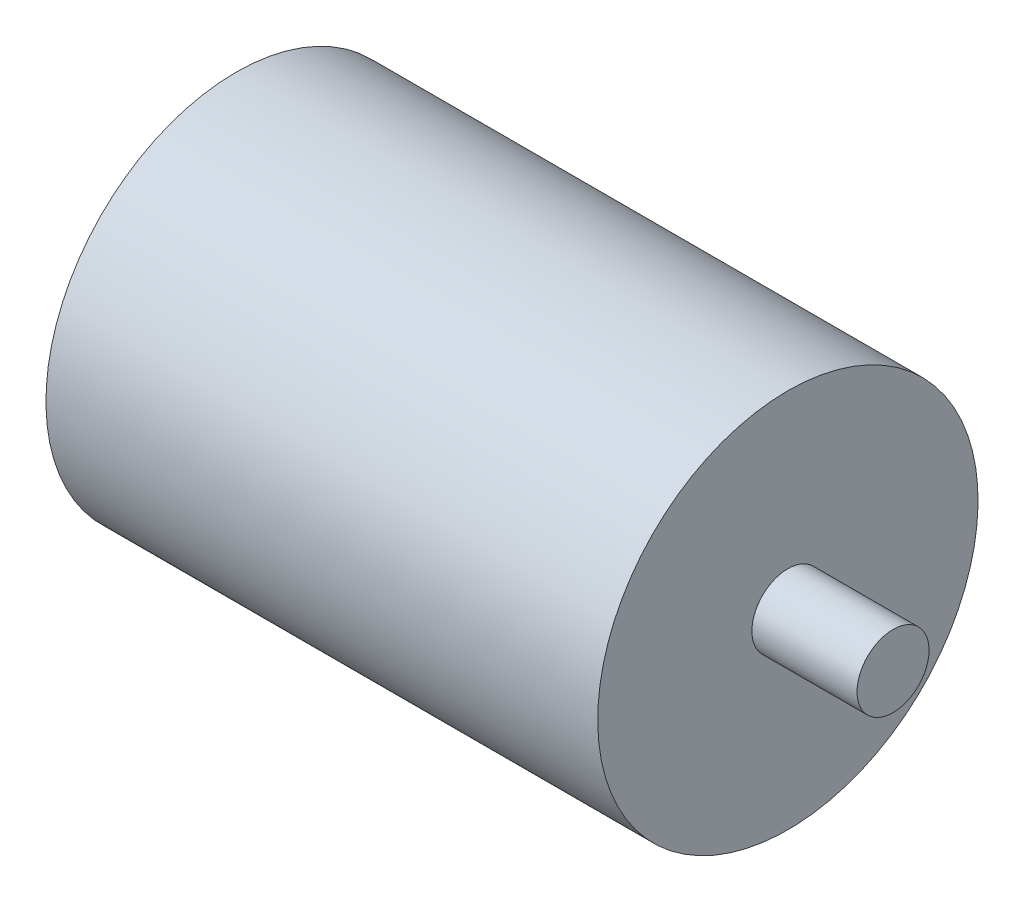
SolidWorks part; units mm, degrees
ref_plane "Front Plane" through (0, 0, 0) normal (0, 0, 1) x (1, 0, 0)
ref_plane "Top Plane" through (0, 0, 0) normal (0, 1, 0) x (1, 0, 0)
ref_plane "Right Plane" through (0, 0, 0) normal (1, 0, 0) x (0, 0, -1)
sketch "Sketch1" plane through (0, 0, 0) normal (0, 0, 1) x (1, 0, 0)
  line L0 (-48.641, 0) -> (48.641, 0)
  point P4 (0, 0)
  dimension "D1" = 97.282
sweep "Sweep1" add path "Sketch1" circular profile diameter 67.056 parameters "D3"=67.056
sketch "Sketch11" plane through (0, 0, 0) normal (0, 0, 1) x (1, 0, 0)
  line L0 (48.641, 0) -> (67.183, 0)
  line L1 (48.641, -33.528) -> (48.641, 33.528) construction
  dimension "D1" = 67.183
sweep "Sweep2" add path "Sketch11" circular profile diameter 12.7 parameters "D3"=12.7
sketch "Sketch30" plane through (0, 0, 0) normal (0, 0, 1) x (1, 0, 0)
  line L0 (-48.641, 0) -> (-67.183, 0)
  line L1 (-48.641, 33.528) -> (-48.641, -33.528) construction
  dimension "D1" = 67.183
sweep "Sweep3" add path "Sketch30" circular profile diameter 12.7 parameters "D3"=12.7
